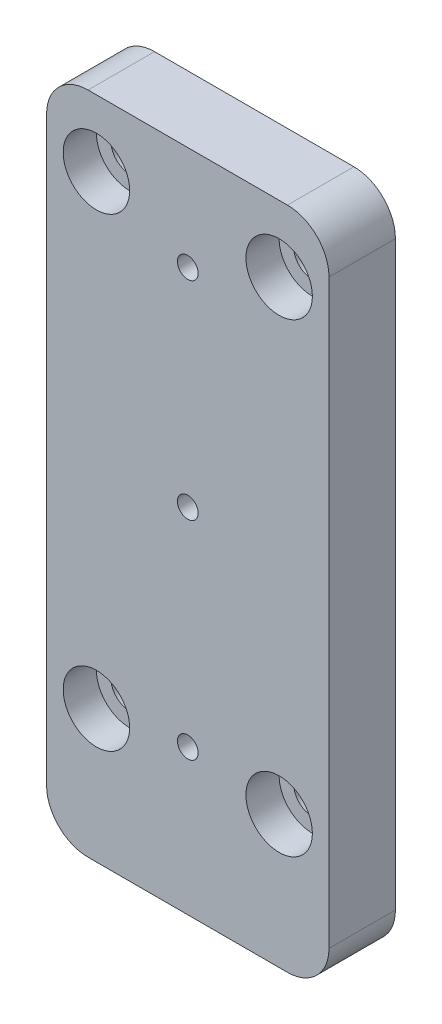
SolidWorks part; units mm, degrees
ref_plane "Front" through (0, 0, 0) normal (0, 0, 1) x (1, 0, 0)
ref_plane "Top" through (0, 0, 0) normal (0, 1, 0) x (1, 0, 0)
ref_plane "Right" through (0, 0, 0) normal (1, 0, 0) x (0, 0, -1)
sketch "Esquisse1" plane through (0, 0, 0) normal (0, 0, 1) x (1, 0, 0)
  line L1 (0, 0) -> (34, 0)
  line L2 (0, 0) -> (0, 80)
  line L3 (0, 80) -> (34, 80)
  line L4 (34, 0) -> (34, 80)
  dimension "D1" = 34
  dimension "D2" = 80
extrude "Boss.-Extru.1" add sketch "Esquisse1" along normal blind 8
sketch "Esquisse2" plane through (0, 0, 8) normal (0, 0, 1) x (1, 0, 0)
  line L0 (17, 0) -> (17, 80) construction
  line L1 (0, 0) -> (34, 0) construction
  line L2 (34, 80) -> (0, 80) construction
  circle A0 centre (17, 17.5) radius 1.25
  circle A1 centre (17, 42.5) radius 1.25
  circle A2 centre (17, 67.5) radius 1.25
  circle A3 centre (17, 92.5) radius 1.25
  circle A4 centre (17, 117.5) radius 1.25
  circle A5 centre (17, 142.5) radius 1.25
  circle A6 centre (17, 167.5) radius 1.25
  circle A7 centre (17, 192.5) radius 1.25
  dimension "D1" = 17.5
  dimension "D2" = 2.5
  dimension "D4" = 25
  dimension "D3" = 8
extrude "Enlèv. mat.-Extru.1" cut sketch "Esquisse2" against normal through all both and the other way through all
sketch "Esquisse3" plane through (0, 0, 8) normal (0, 0, 1) x (1, 0, 0)
  line L0 (17, 0) -> (17, 80) construction
  line L1 (0, 0) -> (34, 0) construction
  line L2 (34, 80) -> (0, 80) construction
  line L3 (0, 44) -> (34, 44) construction
  line L5 (34, 0) -> (34, 80) construction
  line L6 (0, 80) -> (0, 0) construction
  circle A0 centre (6, 16) radius 2.25
  circle A1 centre (28, 16) radius 2.25
  circle A2 centre (28, 72) radius 2.25
  circle A3 centre (6, 72) radius 2.25
  dimension "D1" = 22
  dimension "D2" = 16
  dimension "D3" = 4.5
  dimension "D4" = 56
extrude "Enlèv. mat.-Extru.2" cut sketch "Esquisse3" against normal through all both and the other way through all
sketch "Esquisse4" plane through (0, 0, 8) normal (0, 0, 1) x (1, 0, 0)
  circle A0 centre (6, 16) radius 4
  circle A1 centre (28, 16) radius 4
  circle A2 centre (6, 72) radius 4
  circle A3 centre (28, 72) radius 4
  dimension "D1" = 8
extrude "Enlèv. mat.-Extru.3" cut sketch "Esquisse4" against normal blind 4
fillet "Congé1" radius 5 4 edges at (0, 80, 4) (34, 80, 4) (34, 0, 4) (0, 0, 4)
